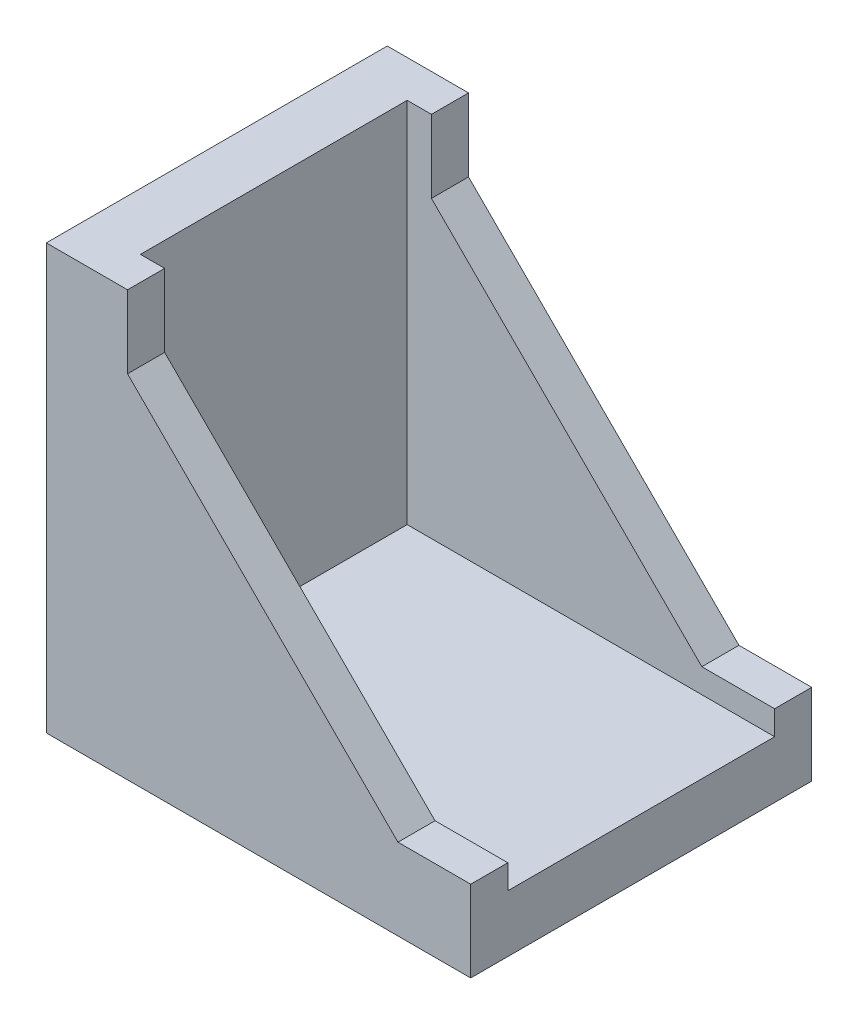
SolidWorks part; units mm, degrees
ref_plane "Alzado" through (0, 0, 0) normal (0, 0, 1) x (1, 0, 0)
ref_plane "Planta" through (0, 0, 0) normal (0, 1, 0) x (1, 0, 0)
ref_plane "Vista lateral" through (0, 0, 0) normal (1, 0, 0) x (0, 0, -1)
sketch "Croquis1" plane through (0, 0, 0) normal (0, 0, 1) x (1, 0, 0)
  line L0 (0, 0) -> (0, 32321.5723) construction
  line L1 (0, 0) -> (32321.5723, 0) construction
  line L2 (0, 0) -> (0, 35)
  line L3 (0, 35) -> (6.7, 35)
  line L4 (6.7, 35) -> (6.7, 29)
  line L5 (6.7, 29) -> (29, 6.7)
  line L6 (29, 6.7) -> (35, 6.7)
  line L7 (35, 6.7) -> (35, 0)
  line L8 (35, 0) -> (0, 0)
  point P7 (5.3747, 35)
  point P13 (5.0506, 24.9533)
  point P14 (39.0798, 0)
  dimension "D1" = 35
  dimension "D2" = 6.7
  dimension "D3" = 6
extrude "Saliente-Extruir1" add sketch "Croquis1" along normal mid plane 28.12
sketch "Croquis4" plane through (0, 0, 0) normal (0, 0, 1) x (1, 0, 0)
  line L0 (4.7, 36.6734) -> (4.7, -49963.3266) construction
  line L1 (42.3597, 4.7) -> (-49957.6403, 4.7) construction
  line L2 (0, 35) -> (0, 0) construction
  line L3 (0, 0) -> (35, 0) construction
  line L4 (35, 0) -> (35, 6.7) construction
  line L5 (4.7, 4.7) -> (35, 4.7)
  line L6 (4.7, 4.7) -> (4.7, 35)
  line L7 (4.7, 35) -> (35, 35)
  line L8 (35, 4.7) -> (35, 35)
  line L9 (4.7, 4.7) -> (35, 35) construction
  line L10 (4.7, 35) -> (35, 4.7) construction
  line L11 (6.7, 35) -> (0, 35) construction
  point P12 (19.85, 19.85)
  point P13 (35, 4.7)
  point P16 (4.7, 35)
  dimension "D1" = 4.7
  dimension "D2" = 4.7
extrude "Cortar-Extruir1" cut sketch "Croquis4" against normal mid plane 22
